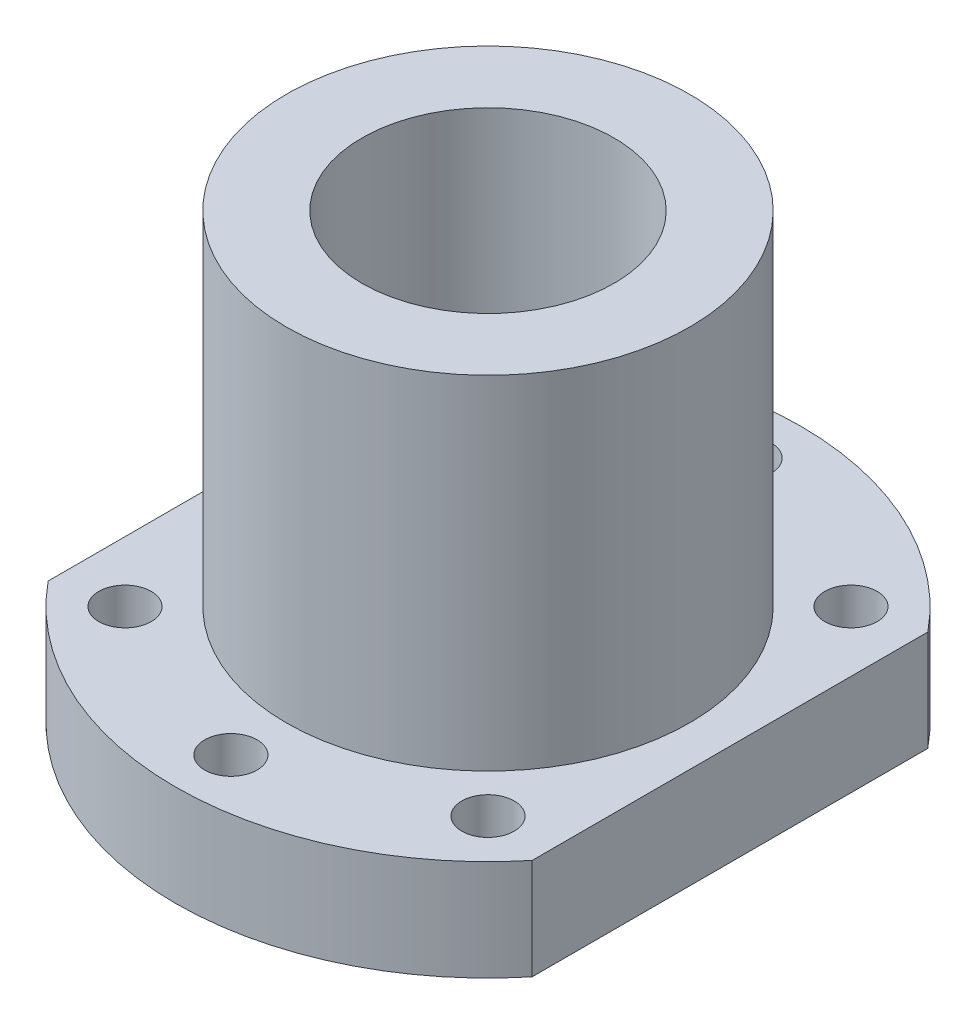
SolidWorks part; units mm, degrees
ref_plane "Front Plane" through (0, 0, 0) normal (0, 0, 1) x (1, 0, 0)
ref_plane "Top Plane" through (0, 0, 0) normal (0, 1, 0) x (1, 0, 0)
ref_plane "Right Plane" through (0, 0, 0) normal (1, 0, 0) x (0, 0, -1)
sketch "Sketch1" plane through (0, 0, 0) normal (0, 1, 0) x (1, 0, 0)
  line L0 (0, 31) -> (0, -31) construction
  line L1 (-24, 19.6214) -> (-24, -19.6214)
  line L2 (24, 19.6214) -> (24, -19.6214)
  line L3 (24, 31) -> (24, -31) construction
  line L4 (-24, 31) -> (-24, -31) construction
  line L6 (-18, 18) -> (18, 18) construction
  line L7 (-18, 18) -> (-18, -18) construction
  line L8 (-18, -18) -> (18, -18) construction
  line L9 (18, 18) -> (18, -18) construction
  line L10 (-18, 18) -> (18, -18) construction
  line L11 (-18, -18) -> (18, 18) construction
  arc A0 (-24, -19.6214) -> (24, -19.6214) centre (0, 0) ccw
  circle A1 centre (0, 0) radius 25.5 construction
  circle A2 centre (18, 18) radius 2.6
  circle A3 centre (0, 25.5) radius 2.6
  circle A4 centre (-18, 18) radius 2.6
  circle A5 centre (-18, -18) radius 2.6
  circle A6 centre (18, -18) radius 2.6
  circle A7 centre (0, -25.5) radius 2.6
  arc A8 (24, 19.6214) -> (-24, 19.6214) centre (0, 0) ccw
  dimension "D1" = 24
  dimension "D3" = 36
  dimension "D5" = 5.2
  dimension "D6" = 51
  dimension "D7" = 62
  dimension "D4" = 36
  dimension "D2" = 24
extrude "Boss-Extrude1" add sketch "Sketch1" along normal blind 10
sketch "Sketch2" plane through (0, 10, 0) normal (0, 1, 0) x (1, 0, 0)
  circle A0 centre (0, 0) radius 20
  dimension "D1" = 40
extrude "Boss-Extrude2" add sketch "Sketch2" along normal blind 34
sketch "Sketch3" plane through (0, 44, 0) normal (0, 1, 0) x (1, 0, 0)
  circle A0 centre (0, 0) radius 12.5
  dimension "D1" = 25
extrude "Cut-Extrude1" cut sketch "Sketch3" against normal up to next
